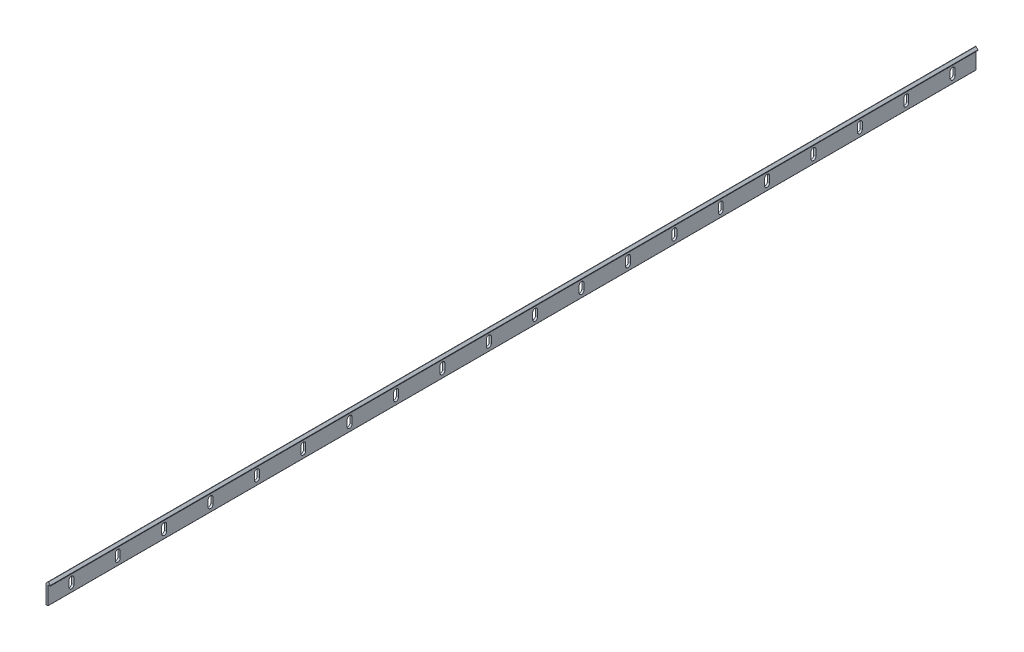
SolidWorks part; units mm, degrees
material "6061-T6 (SS)"
ref_plane "Front Plane" through (0, 0, 0) normal (0, 0, 1) x (1, 0, 0)
ref_plane "Top Plane" through (0, 0, 0) normal (0, 1, 0) x (1, 0, 0)
ref_plane "Right Plane" through (0, 0, 0) normal (1, 0, 0) x (0, 0, -1)
sketch "Sketch1" plane through (0, 0, 0) normal (0, 0, 1) x (1, 0, 0)
  line L0 (0, 0.3) -> (0, 20.125)
  line L1 (0.0879, 20.3371) -> (2.1629, 22.4121)
  line L2 (2.5871, 22.4121) -> (4.6621, 20.3371)
  line L3 (4.75, 20.125) -> (4.75, 19.85)
  line L4 (4.45, 19.55) -> (2.375, 19.55)
  line L5 (2.375, 19.55) -> (2.375, 0.3)
  line L6 (2.075, 0) -> (0.3, 0)
  arc A0 (4.75, 19.85) -> (4.45, 19.55) centre (4.45, 19.85) cw
  arc A1 (4.6621, 20.3371) -> (4.75, 20.125) centre (4.45, 20.125) cw
  arc A2 (0, 20.125) -> (0.0879, 20.3371) centre (0.3, 20.125) cw
  arc A3 (2.1629, 22.4121) -> (2.5871, 22.4121) centre (2.375, 22.2) cw
  arc A4 (0, 0.3) -> (0.3, 0) centre (0.3, 0.3) ccw
  arc A5 (2.375, 0.3) -> (2.075, 0) centre (2.075, 0.3) cw
  point P10 (4.75, 19.55)
  point P13 (4.75, 20.2493)
  point P16 (0, 20.2493)
  point P21 (0, 0)
  point P24 (2.375, 0)
  dimension "D4" = 0.3
  dimension "D6" = 0.3
  dimension "D1" = 2.375
  dimension "D2" = 19.55
  dimension "D3" = 2.375
  dimension "D5" = 22.5
extrude "Boss-Extrude1" add sketch "Sketch1" along normal blind 1000
sketch "Sketch2" plane through (2.375, 0, 0) normal (1, 0, 0) x (0, 0, -1)
  line L0 (-25, 12.7) -> (-25, 6) construction
  line L1 (-22.35, 12.7) -> (-22.35, 6)
  line L2 (-27.65, 12.7) -> (-27.65, 6)
  line L3 (0, 0.3) -> (0, 19.55) construction
  line L4 (-1000, 0) -> (0, 0) construction
  arc A0 (-22.35, 12.7) -> (-27.65, 12.7) centre (-25, 12.7) ccw
  arc A1 (-27.65, 6) -> (-22.35, 6) centre (-25, 6) ccw
  point P2 (-25, 9.35)
  dimension "D1" = 25
  dimension "D2" = 5.3
  dimension "D3" = 6.7
  dimension "D4" = 6
extrude "Cut-Extrude1" cut sketch "Sketch2" against normal through all
pattern_linear "LPattern1" count 20 spacing 50 along (0, 0, 1) of "Cut-Extrude1"
